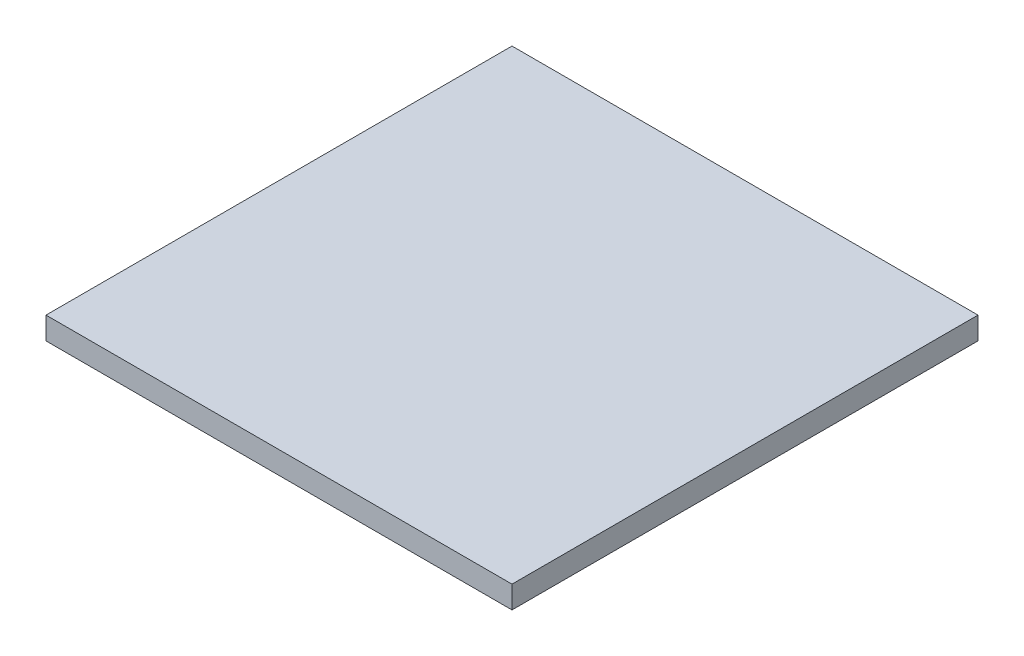
SolidWorks part; units mm, degrees
ref_plane "Front Plane" through (0, 0, 0) normal (0, 0, 1) x (1, 0, 0)
ref_plane "Top Plane" through (0, 0, 0) normal (0, 1, 0) x (1, 0, 0)
ref_plane "Right Plane" through (0, 0, 0) normal (1, 0, 0) x (0, 0, -1)
sketch "Sketch1" plane through (0, 0, 0) normal (0, 1, 0) x (1, 0, 0)
  line L1 (-125, -125) -> (125, -125)
  line L2 (-125, -125) -> (-125, 125)
  line L3 (-125, 125) -> (125, 125)
  line L4 (125, -125) -> (125, 125)
  line L5 (-125, -125) -> (125, 125) construction
  line L6 (-125, 125) -> (125, -125) construction
  point P0 (0, 0)
  dimension "D1" = 250
  dimension "D2" = 250
extrude "Boss-Extrude1" add sketch "Sketch1" along normal blind 12
sketch "Sketch2" plane through (0, 0, 0) normal (0, -1, 0) x (1, 0, 0)
  line L0 (-125, 0) -> (125, 0) construction
  line L1 (-125, -125) -> (-125, 125) construction
  line L2 (125, 125) -> (125, -125) construction
  line L3 (0, 125) -> (0, -125) construction
  line L4 (-125, 125) -> (125, 125) construction
  line L5 (125, -125) -> (-125, -125) construction
  circle A0 centre (-97.5, 45.5) radius 3.5
  circle A1 centre (-73.5, 45.5) radius 3.5
  circle A16 centre (-97.5, 27.5) radius 3.5
  circle A17 centre (-73.5, 27.5) radius 3.5
  circle A18 centre (-73.5, -27.5) radius 3.5
  circle A19 centre (-97.5, -27.5) radius 3.5
  circle A20 centre (-73.5, -45.5) radius 3.5
  circle A21 centre (-97.5, -45.5) radius 3.5
  circle A22 centre (97.5, -45.5) radius 3.5
  circle A23 centre (73.5, -45.5) radius 3.5
  circle A24 centre (97.5, -27.5) radius 3.5
  circle A25 centre (73.5, -27.5) radius 3.5
  circle A26 centre (73.5, 27.5) radius 3.5
  circle A27 centre (97.5, 27.5) radius 3.5
  circle A28 centre (73.5, 45.5) radius 3.5
  circle A29 centre (97.5, 45.5) radius 3.5
  dimension "D1" = 97.5
  dimension "D2" = 45.5
  dimension "D3" = 7
  dimension "D5" = 24
  dimension "D7" = 18
  dimension "D4" = 2
  dimension "D6" = 2
extrude "Cut-Extrude1" cut sketch "Sketch2" against normal blind 3
